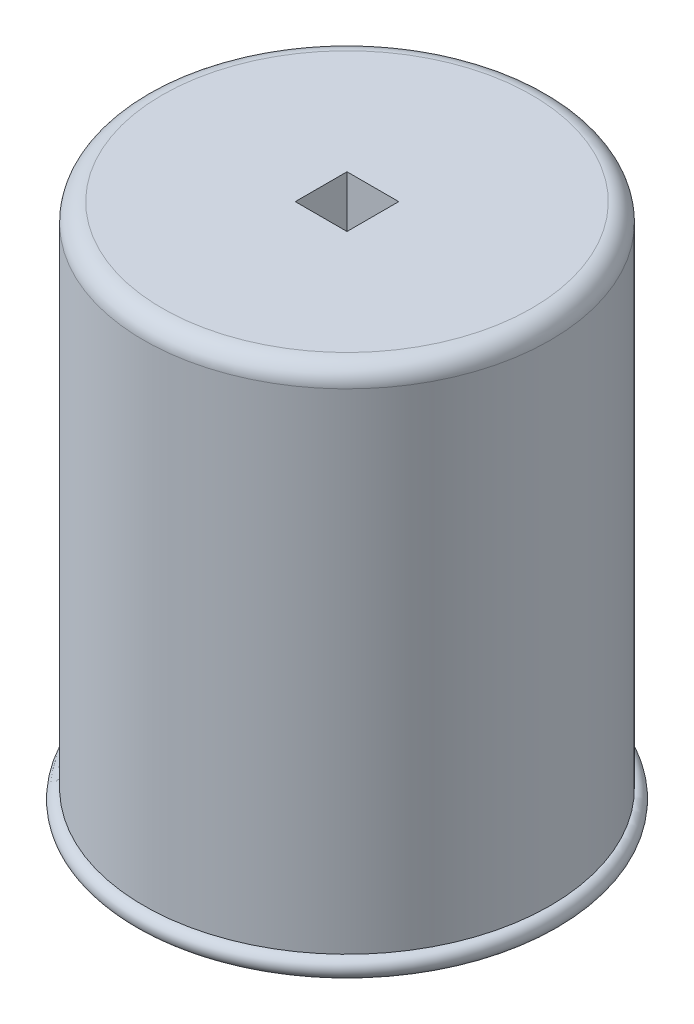
SolidWorks part; units mm, degrees
ref_plane "Front Plane" through (0, 0, 0) normal (0, 0, 1) x (1, 0, 0)
ref_plane "Top Plane" through (0, 0, 0) normal (0, 1, 0) x (1, 0, 0)
ref_plane "Right Plane" through (0, 0, 0) normal (1, 0, 0) x (0, 0, -1)
sketch "Sketch1" plane through (0, 0, 0) normal (0, 0, 1) x (1, 0, 0)
  line L0 (0, 0) -> (0, 40)
  line L1 (0, 40) -> (-110, 40)
  line L2 (-110, 40) -> (-110, -235)
  line L4 (-105, -240) -> (-105, 35)
  line L5 (-105, 35) -> (-28, 35)
  line L6 (-28, 35) -> (-28, -225)
  line L7 (-28, -225) -> (-5, -225)
  line L8 (-5, -225) -> (-5, -220)
  line L9 (-5, -220) -> (-23, -220)
  line L10 (-23, -220) -> (-23, -149)
  line L11 (-23, -149) -> (-5, -149)
  line L12 (-5, -149) -> (-5, -144)
  line L13 (-5, -144) -> (-23, -144)
  line L14 (-23, -144) -> (-23, 0)
  line L15 (-23, 0) -> (0, 0)
  arc A0 (-105, -240) -> (-110, -235) centre (-110, -240) cw
  point P11 (0, 20)
  dimension "D2" = 275
  dimension "D3" = 5
  dimension "D4" = 5
  dimension "D5" = 77
  dimension "D6" = 28
  dimension "D7" = 23
  dimension "D8" = 5
  dimension "D9" = 5
  dimension "D10" = 5
  dimension "D11" = 71
  dimension "D12" = 40
  dimension "D13" = 260
  dimension "D14" = 18
  dimension "D15" = 18
  dimension "D16" = 275
revolve "Revolve2" add sketch "Sketch1" angle 360 about L0
sketch "Sketch3" plane through (0, 40, 0) normal (0, 1, 0) x (1, 0, 0)
  line L1 (-14, 14) -> (14, 14)
  line L2 (-14, 14) -> (-14, -14)
  line L3 (-14, -14) -> (14, -14)
  line L4 (14, 14) -> (14, -14)
  line L5 (-14, 14) -> (14, -14) construction
  line L6 (-14, -14) -> (14, 14) construction
  point P0 (0, 0)
  dimension "D1" = 28
  dimension "D2" = 28
extrude "Cut-Extrude2" cut sketch "Sketch3" against normal up to next
ref_plane "Plane2" through (0, -214.5, 0) normal (0, 1, 0) x (1, 0, 0)
sketch "Sketch6" plane through (0, -214.5, 0) normal (0, 1, 0) x (1, 0, 0)
  line L0 (0, -28) -> (0, -25.5)
  line L1 (7.3608, -24.4145) -> (6.6392, -22.0209)
  line L2 (6.6392, 22.0209) -> (7.3608, 24.4145)
  line L3 (0, 25.5) -> (0, 28)
  circle A0 centre (0, 0) radius 28 construction
  arc A1 (0, -25.5) -> (7.3608, -24.4145) centre (0, 0) ccw
  arc A2 (6.6392, -22.0209) -> (6.6392, 22.0209) centre (0, 0) ccw
  circle A4 centre (0, 0) radius 28 construction
  arc A5 (0, 28) -> (0, -28) centre (0, 0) cw
  arc A7 (0, 25.5) -> (7.3608, 24.4145) centre (0, 0) cw
  point P15 (0, -26.75)
  point P19 (7, -23.2177)
  point P20 (7, 23.2177)
  dimension "D7" = 23
  dimension "D1" = 2.5
  dimension "D2" = 2.5
  dimension "D3" = 2.5
  dimension "D4" = 2.5
  dimension "D5" = 7
  dimension "D6" = 7
extrude "Cut-Extrude3" cut sketch "Sketch6" along normal blind 60
sketch "Sketch7" plane through (0, -149, 0) normal (0, -1, 0) x (1, 0, 0)
  line L1 (11.5, 2.5) -> (16.5, 2.5)
  line L2 (11.5, 2.5) -> (11.5, -2.5)
  line L3 (11.5, -2.5) -> (16.5, -2.5)
  line L4 (16.5, 2.5) -> (16.5, -2.5)
  line L5 (11.5, 2.5) -> (16.5, -2.5) construction
  line L6 (11.5, -2.5) -> (16.5, 2.5) construction
  point P0 (14, 0)
  dimension "D3" = 14
  dimension "D1" = 5
  dimension "D2" = 5
extrude "Cut-Extrude4" cut sketch "Sketch7" against normal up to next
fillet "Fillet1" radius 10 1 edges at (110, 40, 0)
